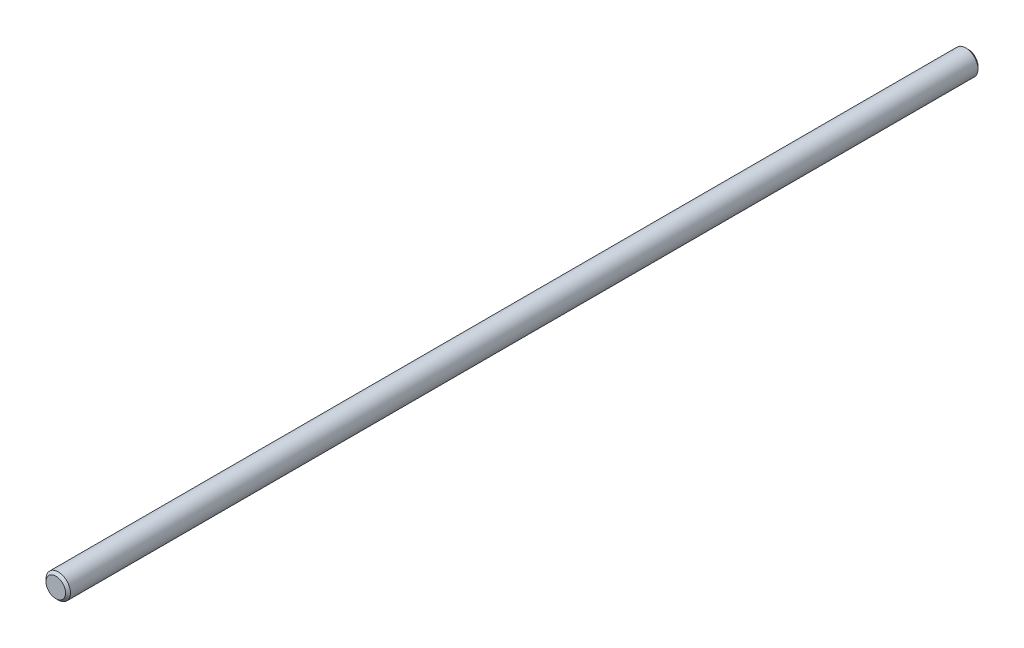
SolidWorks part; units mm, degrees
ref_plane "Front" through (0, 0, 0) normal (0, 0, 1) x (1, 0, 0)
ref_plane "Top" through (0, 0, 0) normal (0, 1, 0) x (1, 0, 0)
ref_plane "Right" through (0, 0, 0) normal (1, 0, 0) x (0, 0, -1)
sketch "Sketch1" plane through (0, 0, 0) normal (0, 0, 1) x (1, 0, 0)
  circle A0 centre (0, 0) radius 4.7625
  dimension "Diameter" = 9.525
sketch "Sketch2" plane through (0, 0, 0) normal (1, 0, 0) x (0, 0, -1)
  line L0 (-177.8, 0) -> (177.8, 0) construction
  line L1 (-127, 4.7625) -> (-127, -4.7625) construction
  line L2 (5.2387, 0) -> (-5.2387, 0) construction
  line L3 (127, 4.7625) -> (127, -4.7625) construction
  line L4 (-177.8, 4.7625) -> (-177.8, -4.7625) construction
  line L5 (177.8, 4.7625) -> (177.8, -4.7625) construction
  point P3 (-127, 0)
  point P8 (0, 0)
  point P9 (127, 0)
  point P15 (-177.8, 0)
  point P18 (177.8, 0)
  dimension "D1" = 9.525
  dimension "Length" = 355.6
  dimension "D2" = 50.8
  dimension "D3" = 50.8
sketch "Sketch3" plane through (0, 0, 0) normal (0, 0, 1) x (1, 0, 0)
  circle A0 centre (0, 0) radius 4.7625
  dimension "D1" = 9.525
extrude "Boss-Extrude1" add sketch "Sketch3" along normal mid plane 355.6
chamfer "Chamfer1" distance 0.9525 angle 45 2 edges at (4.7625, 0, -177.8) (4.7625, 0, 177.8)
equation "\"D1@Sketch3\" = \"Diameter@Sketch1\""
equation "\"D1@Boss-Extrude1\"=\"Length@Sketch2\""
equation "\"D1@Chamfer1\" = \"Diameter@Sketch1\" * .1"
equation "\"D1@Sketch2\" = \"Diameter@Sketch1\""
